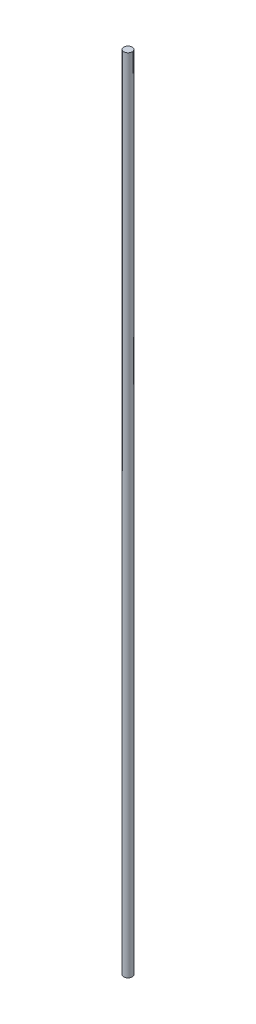
SolidWorks part; units mm, degrees
ref_plane "Front Plane" through (0, 0, 0) normal (0, 0, 1) x (1, 0, 0)
ref_plane "Top Plane" through (0, 0, 0) normal (0, 1, 0) x (1, 0, 0)
ref_plane "Right Plane" through (0, 0, 0) normal (1, 0, 0) x (0, 0, -1)
sketch "Sketch1" plane through (0, 0, 0) normal (0, 1, 0) x (1, 0, 0)
  circle A0 centre (0, 0) radius 1.5875
  dimension "D1" = 3.175
extrude "Boss-Extrude1" add sketch "Sketch1" along normal blind 304.8
